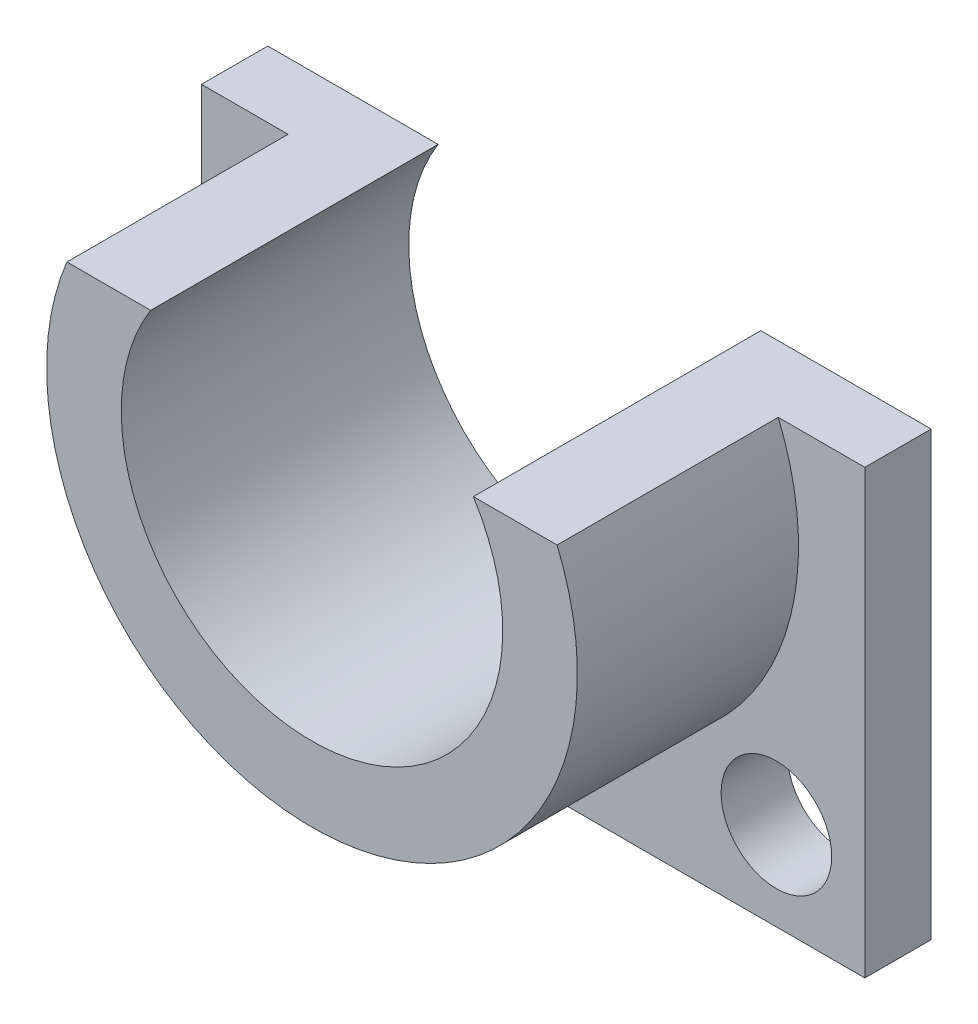
SolidWorks part; units mm, degrees
ref_plane "Front Plane" through (0, 0, 0) normal (0, 0, 1) x (1, 0, 0)
ref_plane "Top Plane" through (0, 0, 0) normal (0, 1, 0) x (1, 0, 0)
ref_plane "Right Plane" through (0, 0, 0) normal (1, 0, 0) x (0, 0, -1)
sketch "Sketch1" plane through (0, 0, 0) normal (0, 0, 1) x (1, 0, 0)
  line L0 (19.05, 57.15) -> (19.05, 31.75)
  line L1 (19.05, 31.75) -> (-19.05, 31.75)
  line L2 (-19.05, 31.75) -> (-19.05, 57.15)
  line L3 (-19.05, 57.15) -> (-9.2658, 57.15)
  line L4 (9.2658, 57.15) -> (19.05, 57.15)
  arc A1 (-9.2658, 57.15) -> (9.2658, 57.15) centre (0, 51.308) ccw
  circle A2 centre (0, 51.308) radius 11.176 construction
  point P6 (0, 31.75)
  dimension "D4" = 10.9537
  dimension "D1" = 38.1
  dimension "D2" = 31.75
  dimension "D3" = 25.4
extrude "Boss-Extrude1" add sketch "Sketch1" along normal blind 3.81
sketch "Sketch2" plane through (0, 0, 3.81) normal (0, 0, 1) x (1, 0, 0)
  line L5 (19.05, 57.15) -> (9.2658, 57.15)
  line L6 (-9.2658, 57.15) -> (-19.05, 57.15)
  line L7 (-19.05, 57.15) -> (-19.05, 31.75)
  line L8 (-19.05, 31.75) -> (19.05, 31.75)
  line L9 (19.05, 31.75) -> (19.05, 57.15)
  line L10 (14.0758, 57.15) -> (9.2658, 57.15)
  line L11 (-9.2658, 57.15) -> (-14.0758, 57.15)
  arc A0 (14.0758, 57.15) -> (-14.0758, 57.15) centre (0, 51.308) cw
  arc A1 (-9.2658, 57.15) -> (9.2658, 57.15) centre (0, 51.308) ccw
  arc A2 (-9.2658, 57.15) -> (9.2658, 57.15) centre (0, 51.308) ccw
  dimension "D2" = 15.24
  dimension "D1" = 0
extrude "Boss-Extrude2" add sketch "Sketch2" along normal blind 12.7
sketch "Sketch3" plane through (0, 0, 3.81) normal (0, 0, 1) x (1, 0, 0)
  line L0 (0, 0) -> (0, 40.3543) construction
  line L1 (-19.05, 31.75) -> (19.05, 31.75) construction
  line L2 (-19.05, 57.15) -> (-19.05, 31.75) construction
  circle A0 centre (-13.97, 36.83) radius 3.175
  arc A1 (-9.2658, 57.15) -> (9.2658, 57.15) centre (0, 51.308) ccw construction
  circle A2 centre (13.97, 36.83) radius 3.175
  dimension "D1" = 6.35
  dimension "D2" = 5.08
  dimension "D3" = 5.08
extrude "Cut-Extrude1" cut sketch "Sketch3" against normal up to surface (3.81 mm away) up to face at (0, 45.884, 0)
